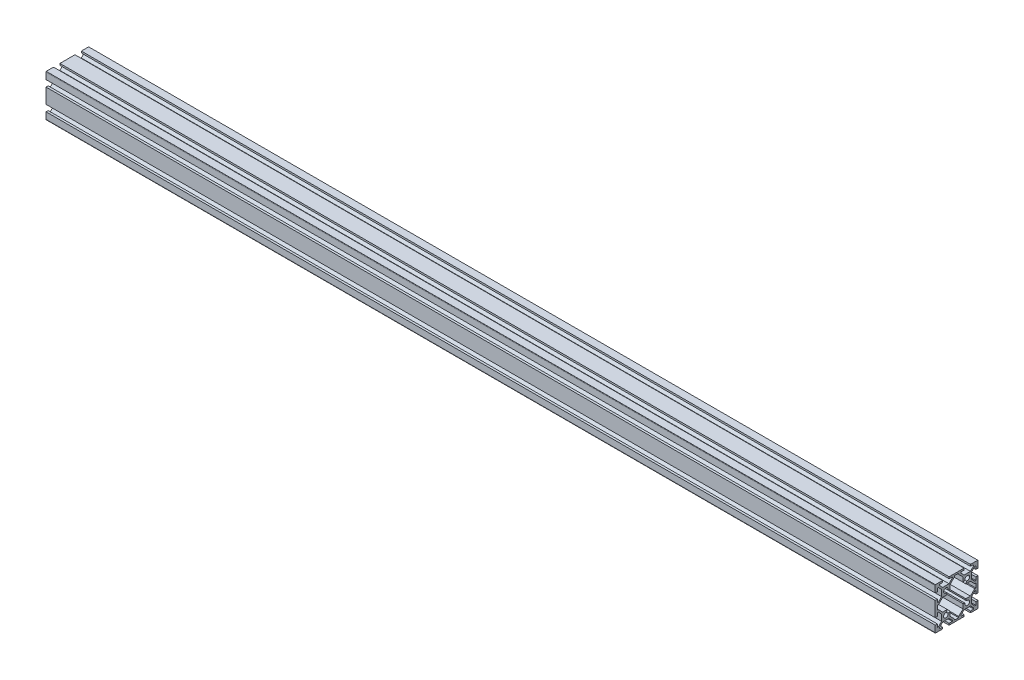
SolidWorks part; units mm, degrees
ref_plane "Front Plane" through (0, 0, 0) normal (0, 0, 1) x (1, 0, 0)
ref_plane "Top Plane" through (0, 0, 0) normal (0, 1, 0) x (1, 0, 0)
ref_plane "Right Plane" through (0, 0, 0) normal (1, 0, 0) x (0, 0, -1)
sketch "Sketch1" plane through (0, 0, 0) normal (1, 0, 0) x (0, 0, -1)
  line L0 (-16.9393, 2) -> (-18, 2)
  line L1 (-12.9393, 6) -> (-16.9393, 2)
  line L2 (-8.6667, 6) -> (-12.9393, 6)
  line L3 (-9.3359, 8.0078) -> (-8.6667, 6)
  line L4 (-6, 8.6667) -> (-8.0078, 9.3359)
  line L5 (-6, 12.9393) -> (-6, 8.6667)
  line L6 (-2, 16.9393) -> (-6, 12.9393)
  line L7 (-2, 18) -> (-2, 16.9393)
  line L8 (2, 18) -> (-2, 18)
  line L9 (2, 16.9393) -> (2, 18)
  line L10 (6, 12.9393) -> (2, 16.9393)
  line L11 (6, 8.6667) -> (6, 12.9393)
  line L12 (8.0078, 9.3359) -> (6, 8.6667)
  line L13 (8.6667, 6) -> (9.3359, 8.0078)
  line L14 (12.9393, 6) -> (8.6667, 6)
  line L15 (16.9393, 2) -> (12.9393, 6)
  line L16 (18, 2) -> (16.9393, 2)
  line L17 (18, -2) -> (18, 2)
  line L18 (16.9393, -2) -> (18, -2)
  line L19 (12.9393, -6) -> (16.9393, -2)
  line L20 (8.6667, -6) -> (12.9393, -6)
  line L21 (9.3359, -8.0078) -> (8.6667, -6)
  line L22 (6, -8.6667) -> (8.0078, -9.3359)
  line L23 (6, -12.9393) -> (6, -8.6667)
  line L24 (2, -16.9393) -> (6, -12.9393)
  line L25 (2, -18) -> (2, -16.9393)
  line L26 (-2, -18) -> (2, -18)
  line L27 (-2, -16.9393) -> (-2, -18)
  line L28 (-6, -12.9393) -> (-2, -16.9393)
  line L29 (-6, -8.6667) -> (-6, -12.9393)
  line L30 (-8.0078, -9.3359) -> (-6, -8.6667)
  line L31 (-8.6667, -6) -> (-9.3359, -8.0078)
  line L32 (-12.9393, -6) -> (-8.6667, -6)
  line L33 (-16.9393, -2) -> (-12.9393, -6)
  line L34 (-18, -2) -> (-16.9393, -2)
  line L35 (-18, 2) -> (-18, -2)
  line L36 (-20, 19) -> (-20, 13)
  line L37 (-20, 13) -> (-18, 13)
  line L38 (-18, 13) -> (-18, 16)
  line L39 (-18, 16) -> (-17.0607, 16)
  line L40 (-17.0607, 16) -> (-14, 12.9393)
  line L41 (-14, 12.9393) -> (-14, 7.0607)
  line L45 (-14, 7.0607) -> (-17.0607, 4)
  line L46 (-17.0607, 4) -> (-18, 4)
  line L47 (-18, 4) -> (-18, 7)
  line L48 (-18, 7) -> (-20, 7)
  line L49 (-20, 7) -> (-20, -7)
  line L50 (-20, -7) -> (-18, -7)
  line L51 (-18, -7) -> (-18, -4)
  line L52 (-18, -4) -> (-17.0607, -4)
  line L53 (-17.0607, -4) -> (-14, -7.0607)
  line L54 (-14, -7.0607) -> (-14, -12.9393)
  line L58 (-14, -12.9393) -> (-17.0607, -16)
  line L59 (-17.0607, -16) -> (-18, -16)
  line L60 (-18, -16) -> (-18, -13)
  line L61 (-18, -13) -> (-20, -13)
  line L62 (-20, -13) -> (-20, -19)
  line L63 (-19.8, -19.6) -> (-13, -19.6)
  line L64 (-13, -19.6) -> (-13, -18)
  line L65 (-13, -18) -> (-16, -18)
  line L66 (-16, -18) -> (-16, -17.0607)
  line L67 (-16, -17.0607) -> (-12.9393, -14)
  line L68 (-12.9393, -14) -> (-7.0607, -14)
  line L72 (-7.0607, -14) -> (-4, -17.0607)
  line L73 (-4, -17.0607) -> (-4, -18)
  line L74 (-4, -18) -> (-7, -18)
  line L75 (-7, -18) -> (-7, -19.6)
  line L76 (-7, -19.6) -> (7, -19.6)
  line L77 (7, -19.6) -> (7, -18)
  line L78 (7, -18) -> (4, -18)
  line L79 (4, -18) -> (4, -17.0607)
  line L80 (4, -17.0607) -> (7.0607, -14)
  line L81 (7.0607, -14) -> (12.9393, -14)
  line L85 (12.9393, -14) -> (16, -17.0607)
  line L86 (16, -17.0607) -> (16, -18)
  line L87 (16, -18) -> (13, -18)
  line L88 (13, -18) -> (13, -19.6)
  line L89 (13, -19.6) -> (19.8, -19.6)
  line L90 (20, -19) -> (20, -13)
  line L91 (20, -13) -> (18, -13)
  line L92 (18, -13) -> (18, -16)
  line L93 (18, -16) -> (17.0607, -16)
  line L94 (17.0607, -16) -> (14, -12.9393)
  line L98 (14, -12.9393) -> (14, -7.0607)
  line L99 (14, -7.0607) -> (17.0607, -4)
  line L100 (17.0607, -4) -> (18, -4)
  line L101 (18, -4) -> (18, -7)
  line L102 (18, -7) -> (20, -7)
  line L103 (20, -7) -> (20, 7)
  line L104 (20, 7) -> (18, 7)
  line L105 (18, 7) -> (18, 4)
  line L106 (18, 4) -> (17.0607, 4)
  line L107 (17.0607, 4) -> (14, 7.0607)
  line L111 (14, 7.0607) -> (14, 12.9393)
  line L112 (14, 12.9393) -> (17.0607, 16)
  line L113 (17.0607, 16) -> (18, 16)
  line L114 (18, 16) -> (18, 13)
  line L115 (18, 13) -> (20, 13)
  line L116 (20, 13) -> (20, 19)
  line L117 (19.8, 19.6) -> (13, 19.6)
  line L118 (13, 19.6) -> (13, 18)
  line L119 (13, 18) -> (16, 18)
  line L120 (16, 18) -> (16, 17.0607)
  line L121 (16, 17.0607) -> (12.9393, 14)
  line L125 (12.9393, 14) -> (7.0607, 14)
  line L126 (7.0607, 14) -> (4, 17.0607)
  line L127 (4, 17.0607) -> (4, 18)
  line L128 (4, 18) -> (7, 18)
  line L129 (7, 18) -> (7, 19.6)
  line L130 (7, 19.6) -> (-7, 19.6)
  line L131 (-7, 19.6) -> (-7, 18)
  line L132 (-7, 18) -> (-4, 18)
  line L133 (-4, 18) -> (-4, 17.0607)
  line L134 (-4, 17.0607) -> (-7.0607, 14)
  line L138 (-7.0607, 14) -> (-12.9393, 14)
  line L139 (-12.9393, 14) -> (-16, 17.0607)
  line L140 (-16, 17.0607) -> (-16, 18)
  line L141 (-16, 18) -> (-13, 18)
  line L142 (-13, 18) -> (-13, 19.6)
  line L143 (-13, 19.6) -> (-19.8, 19.6)
  arc A0 (-20, -19) -> (-19.8, -19.6) centre (-19, -19) ccw
  arc A1 (19.8, -19.6) -> (20, -19) centre (19, -19) ccw
  arc A2 (20, 19) -> (19.8, 19.6) centre (19, 19) ccw
  arc A3 (-19.8, 19.6) -> (-20, 19) centre (-19, 19) ccw
  arc A4 (-8.0078, 9.3359) -> (-9.3359, 8.0078) centre (-10, 10) ccw
  arc A5 (9.3359, 8.0078) -> (8.0078, 9.3359) centre (10, 10) ccw
  arc A6 (8.0078, -9.3359) -> (9.3359, -8.0078) centre (10, -10) ccw
  arc A7 (-9.3359, -8.0078) -> (-8.0078, -9.3359) centre (-10, -10) ccw
  dimension "A" = 40
  dimension "T" = 39.2
extrude "Boss-Extrude1" add sketch "Sketch1" along normal blind 830
ref_plane "Plane1" through (0, 19.6, 0) normal (0, 1, 0) x (1, 0, 0)
ref_plane "Plane2" through (0, 0, 0) normal (1, 0, 0) x (0, 0, -1)
ref_plane "Plane3" through (830, 0, 0) normal (1, 0, 0) x (0, 0, -1)
ref_plane "Plane4" through (7, 0, 0) normal (1, 0, 0) x (0, 0, -1)
ref_plane "Plane5" through (19, 0, 0) normal (1, 0, 0) x (0, 0, -1)
ref_plane "Plane6" through (31, 0, 0) normal (1, 0, 0) x (0, 0, -1)
ref_plane "Plane7" through (43, 0, 0) normal (1, 0, 0) x (0, 0, -1)
ref_plane "Plane8" through (55, 0, 0) normal (1, 0, 0) x (0, 0, -1)
sketch "Sketch2" [suppressed] plane through (7, 0, 0) normal (1, 0, 0) x (0, 0, -1)
  line L0 (10, -19.6) -> (12.75, -19.6)
  line L1 (12.75, -19.6) -> (12.75, 14)
  line L2 (12.75, 14) -> (14.75, 14)
  line L3 (14.75, 14) -> (14.75, 19.6)
  line L4 (14.75, 19.6) -> (10, 19.6)
  line L5 (10, 19.6) -> (10, -19.6) construction
  line L6 (10, 19.6) -> (10, -19.6)
  point P6 (10, 0)
  dimension "T" = 39.2
  dimension "FIX_3" = 5.6
  dimension "D1_s" = 9.5
  dimension "D_s" = 5.5
  dimension "FIX_4" = 10
revolve "Cut-Revolve1" [suppressed] cut sketch "Sketch2" angle 360 about L5
mirror "Mirror1" [suppressed] about plane through (0, 0, 0) normal (0, 0, 1)
sketch "Sketch3" [suppressed] plane through (18.5, 0, 0) normal (1, 0, 0) x (0, 0, -1)
  line L0 (10, -19.6) -> (12.75, -19.6)
  line L1 (12.75, -19.6) -> (12.75, 14)
  line L2 (12.75, 14) -> (14.75, 14)
  line L3 (14.75, 14) -> (14.75, 19.6)
  line L4 (14.75, 19.6) -> (10, 19.6)
  line L5 (10, 19.6) -> (10, -19.6) construction
  line L6 (10, 19.6) -> (10, -19.6)
  point P6 (10, 0)
  dimension "T" = 39.2
  dimension "FIX_6" = 5.6
  dimension "D1_s" = 9.5
  dimension "D_s" = 5.5
  dimension "FIX_7" = 10
revolve "Cut-Revolve2" [suppressed] cut sketch "Sketch3" angle 360 about L5
mirror "Mirror2" [suppressed] about plane through (0, 0, 0) normal (0, 0, 1)
sketch "Sketch4" [suppressed] plane through (30, 0, 0) normal (1, 0, 0) x (0, 0, -1)
  line L0 (10, -19.6) -> (12.75, -19.6)
  line L1 (12.75, -19.6) -> (12.75, 14)
  line L2 (12.75, 14) -> (14.75, 14)
  line L3 (14.75, 14) -> (14.75, 19.6)
  line L4 (14.75, 19.6) -> (10, 19.6)
  line L5 (10, 19.6) -> (10, -19.6) construction
  line L6 (10, 19.6) -> (10, -19.6)
  point P6 (10, 0)
  dimension "T" = 39.2
  dimension "FIX_9" = 5.6
  dimension "D1_s" = 9.5
  dimension "D_s" = 5.5
  dimension "FIX_10" = 10
revolve "Cut-Revolve3" [suppressed] cut sketch "Sketch4" angle 360 about L5
mirror "Mirror3" [suppressed] about plane through (0, 0, 0) normal (0, 0, 1)
sketch "Sketch5" [suppressed] plane through (41.5, 0, 0) normal (1, 0, 0) x (0, 0, -1)
  line L0 (10, -19.6) -> (12.75, -19.6)
  line L1 (12.75, -19.6) -> (12.75, 14)
  line L2 (12.75, 14) -> (14.75, 14)
  line L3 (14.75, 14) -> (14.75, 19.6)
  line L4 (14.75, 19.6) -> (10, 19.6)
  line L5 (10, 19.6) -> (10, -19.6) construction
  line L6 (10, 19.6) -> (10, -19.6)
  point P6 (10, 0)
  dimension "T" = 39.2
  dimension "FIX_12" = 5.6
  dimension "D1_s" = 9.5
  dimension "D_s" = 5.5
  dimension "FIX_13" = 10
revolve "Cut-Revolve4" [suppressed] cut sketch "Sketch5" angle 360 about L5
mirror "Mirror4" [suppressed] about plane through (0, 0, 0) normal (0, 0, 1)
sketch "Sketch6" [suppressed] plane through (53, 0, 0) normal (1, 0, 0) x (0, 0, -1)
  line L0 (10, -19.6) -> (12.75, -19.6)
  line L1 (12.75, -19.6) -> (12.75, 14)
  line L2 (12.75, 14) -> (14.75, 14)
  line L3 (14.75, 14) -> (14.75, 19.6)
  line L4 (14.75, 19.6) -> (10, 19.6)
  line L5 (10, 19.6) -> (10, -19.6) construction
  line L6 (10, 19.6) -> (10, -19.6)
  point P6 (10, 0)
  dimension "T" = 39.2
  dimension "FIX_15" = 5.6
  dimension "D1_s" = 9.5
  dimension "D_s" = 5.5
  dimension "FIX_16" = 10
revolve "Cut-Revolve5" [suppressed] cut sketch "Sketch6" angle 360 about L5
mirror "Mirror5" [suppressed] about plane through (0, 0, 0) normal (0, 0, 1)
sketch "Sketch7" [suppressed] plane through (0, 19.6, 0) normal (0, 1, 0) x (1, 0, 0)
  circle A0 centre (7, -10) radius 3.675
  circle A1 centre (7, 10) radius 3.675
  dimension "D" = 7.35
  dimension "AV" = 7
  dimension "FIX_18" = 20
  dimension "FIX_19" = 10
extrude "Cut-Extrude1" [suppressed] cut sketch "Sketch7" against normal blind 39.2
sketch "Sketch8" [suppressed] plane through (0, 19.6, 0) normal (0, 1, 0) x (1, 0, 0)
  circle A0 centre (18.5, -10) radius 3.675
  circle A1 centre (18.5, 10) radius 3.675
  dimension "D" = 7.35
  dimension "BV" = 19
  dimension "FIX_20" = 10
  dimension "FIX_21" = 20
extrude "Cut-Extrude2" [suppressed] cut sketch "Sketch8" against normal blind 39.2
sketch "Sketch9" [suppressed] plane through (0, 19.6, 0) normal (0, 1, 0) x (1, 0, 0)
  circle A0 centre (30, -10) radius 3.675
  circle A1 centre (30, 10) radius 3.675
  dimension "D" = 7.35
  dimension "CV" = 31
  dimension "FIX_22" = 20
  dimension "FIX_23" = 10
extrude "Cut-Extrude3" [suppressed] cut sketch "Sketch9" against normal blind 39.2
sketch "Sketch10" [suppressed] plane through (0, 19.6, 0) normal (0, 1, 0) x (1, 0, 0)
  circle A0 centre (41.5, -10) radius 3.675
  circle A1 centre (41.5, 10) radius 3.675
  dimension "D" = 7.35
  dimension "DV" = 43
  dimension "FIX_24" = 10
  dimension "FIX_25" = 20
extrude "Cut-Extrude4" [suppressed] cut sketch "Sketch10" against normal blind 39.2
sketch "Sketch11" [suppressed] plane through (0, 19.6, 0) normal (0, 1, 0) x (1, 0, 0)
  circle A0 centre (53, -10) radius 3.675
  circle A1 centre (53, 10) radius 3.675
  dimension "D" = 7.35
  dimension "EV" = 55
  dimension "FIX_26" = 10
  dimension "FIX_27" = 20
extrude "Cut-Extrude5" [suppressed] cut sketch "Sketch11" against normal blind 39.2
sketch "Sketch12" [suppressed] plane through (0, 0, 0) normal (1, 0, 0) x (0, 0, -1)
  circle A0 centre (-10, -10) radius 2.1
  circle A1 centre (10, -10) radius 2.1
  circle A2 centre (10, 10) radius 2.1
  circle A3 centre (-10, 10) radius 2.1
  dimension "FIX_28" = 4.2
  dimension "FIX_29" = 20
  dimension "FIX_30" = 20
  dimension "FIX_31" = 10
  dimension "FIX_32" = 10
extrude "Boss-Extrude2" [suppressed] add sketch "Sketch12" along normal blind 15
hole_wizard "Tapped Hole1" [suppressed] positions "Sketch14" profile "Sketch13" tap size "M5x0.8" standard "JIS"
sketch "Sketch14" [suppressed] plane through (0, 0, 0) normal (1, 0, 0) x (0, 0, -1)
  point P0 (10, 10)
  point P2 (-10, 10)
  point P4 (10, -10)
  point P6 (-10, -10)
  dimension "FIX_34" = 20
  dimension "FIX_35" = 20
  dimension "FIX_36" = 10
  dimension "FIX_37" = 10
sketch "Sketch13" [suppressed] plane through (0, 10, -10) normal (0, 1, 0) x (0, 0, 1)
  line L0 (0, 0) -> (0, 15)
  line L1 (0, 15) -> (2.1, 15)
  line L2 (2.1, 15) -> (2.1, 0)
  line L5 (2.1, 0) -> (0, 0)
  line L11 (0, -6.35) -> (0, 107.95) construction
  dimension "Thru Tap Drill Dia." = 4.2
  dimension "Thru Tap Drill Depth" = 15
cosmetic thread "Hole Thread1" [suppressed] parameters "NFIX_2"=15, "NFIX_1"=5
cosmetic thread "Hole Thread2" [suppressed] parameters "NFIX_2"=15, "NFIX_1"=5
cosmetic thread "Hole Thread3" [suppressed] parameters "NFIX_2"=15, "NFIX_1"=5
cosmetic thread "Hole Thread4" [suppressed] parameters "NFIX_2"=15, "NFIX_1"=5
sketch "Sketch15" [suppressed] plane through (100, 0, 0) normal (1, 0, 0) x (0, 0, -1)
  circle A0 centre (-10, -10) radius 2.1
  circle A1 centre (10, -10) radius 2.1
  circle A2 centre (10, 10) radius 2.1
  circle A3 centre (-10, 10) radius 2.1
  dimension "FIX_39" = 4.2
  dimension "FIX_38" = 20
  dimension "FIX_40" = 10
  dimension "FIX_41" = 10
  dimension "FIX_42" = 20
extrude "Boss-Extrude3" [suppressed] add sketch "Sketch15" against normal blind 15
hole_wizard "Tapped Hole2" [suppressed] positions "Sketch17" profile "Sketch16" tap size "M5x0.8" standard "JIS"
sketch "Sketch17" [suppressed] plane through (100, 0, 0) normal (1, 0, 0) x (0, 0, -1)
  point P0 (-10, 10)
  point P2 (10, 10)
  point P4 (-10, -10)
  point P6 (10, -10)
  dimension "FIX_44" = 20
  dimension "FIX_45" = 20
  dimension "FIX_46" = 10
  dimension "FIX_47" = 10
sketch "Sketch16" [suppressed] plane through (100, 10, 10) normal (0, 1, 0) x (0, 0, -1)
  line L0 (0, 0) -> (0, 15)
  line L1 (0, 15) -> (2.1, 15)
  line L2 (2.1, 15) -> (2.1, 0)
  line L5 (2.1, 0) -> (0, 0)
  line L11 (0, -6.35) -> (0, 107.95) construction
  dimension "Thru Tap Drill Dia." = 4.2
  dimension "Thru Tap Drill Depth" = 15
cosmetic thread "Hole Thread5" [suppressed] parameters "NFIX_2"=15, "NFIX_1"=5
cosmetic thread "Hole Thread6" [suppressed] parameters "NFIX_2"=15, "NFIX_1"=5
cosmetic thread "Hole Thread7" [suppressed] parameters "NFIX_2"=15, "NFIX_1"=5
cosmetic thread "Hole Thread8" [suppressed] parameters "NFIX_2"=15, "NFIX_1"=5
sketch "Sketch18" [suppressed] plane through (0, 0, 0) normal (1, 0, 0) x (0, 0, -1)
  circle A1 centre (-10, -10) radius 2.1
  circle A2 centre (10, -10) radius 2.1
  circle A3 centre (10, 10) radius 2.1
  circle A4 centre (-10, 10) radius 2.1
  dimension "FIX_48" = 4.2
  dimension "FIX_49" = 20
  dimension "FIX_50" = 20
  dimension "FIX_51" = 10
  dimension "FIX_52" = 10
extrude "Boss-Extrude4" [suppressed] add sketch "Sketch18" along normal blind 15
sketch "Sketch19" [suppressed] plane through (100, 0, 0) normal (1, 0, 0) x (0, 0, -1)
  circle A0 centre (-10, -10) radius 2.1
  circle A1 centre (10, -10) radius 2.1
  circle A2 centre (10, 10) radius 2.1
  circle A3 centre (-10, 10) radius 2.1
  dimension "FIX_56" = 4.2
  dimension "FIX_54" = 20
  dimension "FIX_55" = 20
  dimension "FIX_57" = 10
  dimension "FIX_58" = 10
extrude "Boss-Extrude5" [suppressed] add sketch "Sketch19" against normal blind 15
hole_wizard "Tapped Hole3" [suppressed] positions "Sketch21" profile "Sketch20" tap size "M5x0.8" standard "JIS"
sketch "Sketch21" [suppressed] plane through (0, 0, 0) normal (1, 0, 0) x (0, 0, -1)
  point P0 (10, 10)
  point P2 (-10, 10)
  point P4 (-10, -10)
  point P6 (10, -10)
  dimension "FIX_60" = 20
  dimension "FIX_61" = 10
  dimension "FIX_62" = 20
  dimension "FIX_63" = 10
sketch "Sketch20" [suppressed] plane through (0, 10, -10) normal (0, 1, 0) x (0, 0, 1)
  line L0 (0, 0) -> (0, 15)
  line L1 (0, 15) -> (2.1, 15)
  line L2 (2.1, 15) -> (2.1, 0)
  line L5 (2.1, 0) -> (0, 0)
  line L11 (0, -6.35) -> (0, 107.95) construction
  dimension "Thru Tap Drill Dia." = 4.2
  dimension "Thru Tap Drill Depth" = 15
cosmetic thread "Hole Thread9" [suppressed] parameters "NFIX_2"=15, "NFIX_1"=5
cosmetic thread "Hole Thread10" [suppressed] parameters "NFIX_2"=15, "NFIX_1"=5
cosmetic thread "Hole Thread11" [suppressed] parameters "NFIX_2"=15, "NFIX_1"=5
cosmetic thread "Hole Thread12" [suppressed] parameters "NFIX_2"=15, "NFIX_1"=5
hole_wizard "Tapped Hole4" [suppressed] positions "Sketch23" profile "Sketch22" tap size "M5x0.8" standard "JIS"
sketch "Sketch23" [suppressed] plane through (100, 0, 0) normal (1, 0, 0) x (0, 0, -1)
  point P0 (-10, 10)
  point P2 (10, 10)
  point P4 (-10, -10)
  point P6 (10, -10)
  dimension "FIX_64" = 20
  dimension "FIX_65" = 20
  dimension "FIX_66" = 10
  dimension "FIX_67" = 10
sketch "Sketch22" [suppressed] plane through (100, 10, 10) normal (0, 1, 0) x (0, 0, -1)
  line L0 (0, 0) -> (0, 15)
  line L1 (0, 15) -> (2.1, 15)
  line L2 (2.1, 15) -> (2.1, 0)
  line L5 (2.1, 0) -> (0, 0)
  line L11 (0, -6.35) -> (0, 107.95) construction
  dimension "Thru Tap Drill Dia." = 4.2
  dimension "Thru Tap Drill Depth" = 15
cosmetic thread "Hole Thread13" [suppressed] parameters "NFIX_2"=15, "NFIX_1"=5
cosmetic thread "Hole Thread14" [suppressed] parameters "NFIX_2"=15, "NFIX_1"=5
cosmetic thread "Hole Thread15" [suppressed] parameters "NFIX_2"=15, "NFIX_1"=5
cosmetic thread "Hole Thread16" [suppressed] parameters "NFIX_2"=15, "NFIX_1"=5
